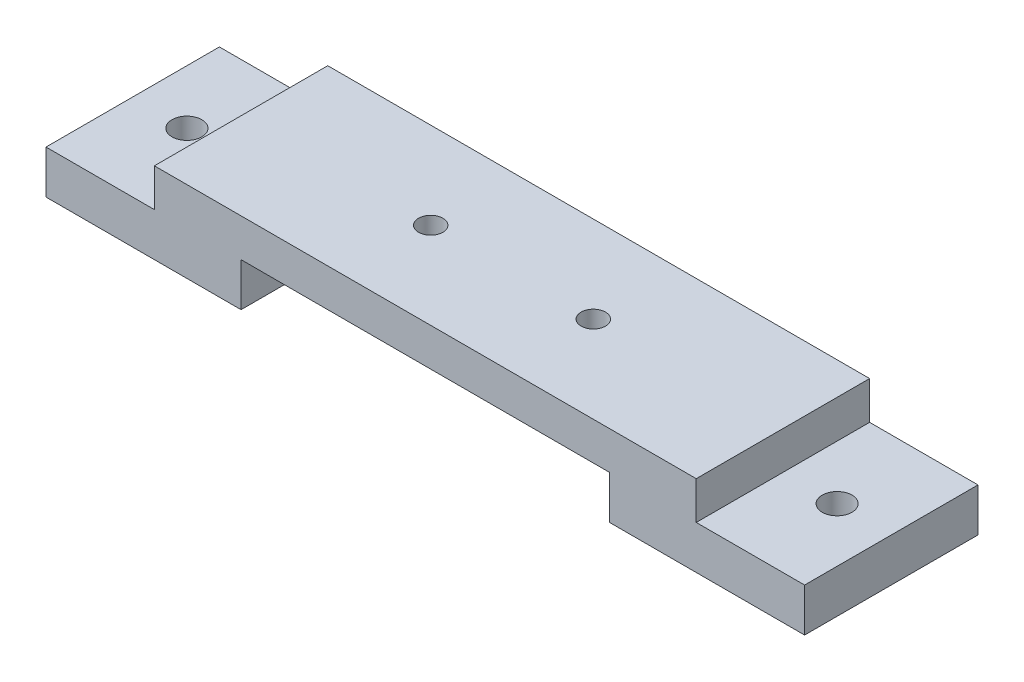
SolidWorks part; units mm, degrees
ref_plane "Ebene vorne" through (0, 0, 0) normal (0, 0, 1) x (1, 0, 0)
ref_plane "Ebene oben" through (0, 0, 0) normal (0, 1, 0) x (1, 0, 0)
ref_plane "Ebene rechts" through (0, 0, 0) normal (1, 0, 0) x (0, 0, -1)
sketch "Skizze1" plane through (0, 0, 0) normal (0, 0, 1) x (1, 0, 0)
  line L0 (-70, 20) -> (-34, 20)
  line L1 (-34, 20) -> (-34, 28)
  line L2 (-34, 28) -> (34, 28)
  line L3 (34, 28) -> (34, 20)
  line L4 (34, 20) -> (70, 20)
  line L5 (70, 20) -> (70, 28)
  line L6 (70, 28) -> (50, 28)
  line L7 (50, 28) -> (50, 35)
  line L8 (50, 35) -> (-50, 35)
  line L9 (-50, 35) -> (-50, 28)
  line L10 (-50, 28) -> (-70, 28)
  line L11 (-70, 28) -> (-70, 20)
  line L12 (34, 20) -> (34, 10) construction
  line L13 (50, 10) -> (70, 10) construction
  line L14 (34, 10) -> (-34, 10) construction
  line L15 (-50, 0) -> (50, 0) construction
  dimension "D2" = 8
  dimension "D3" = 8
  dimension "D4" = 7
extrude "Aufsatz-Linear austragen1" add sketch "Skizze1" against normal blind 32
hole_wizard "Ø4.5 (4.5) Durchmesser Bohrung1" positions "3D-Skizze1" profile "Skizze2" hole size "Ø4.5" standard "ANSI Metrisch" end condition through all
sketch3d "3D-Skizze1"
  line L0 (-34, 28, -16) -> (34, 28, -16) construction
  line L1 (-34, 28, -32) -> (-34, 28, 0) construction
  line L2 (34, 28, -32) -> (34, 28, 0) construction
  point P0 (-15, 28, -16)
  point P2 (15, 28, -16)
  dimension "D1" = 30
  dimension "D2" = 19
sketch "Skizze2" plane through (-15, 28, -16) normal (1, 0, 0) x (0, 0, -1)
  line L0 (0, 0) -> (0, 7)
  line L1 (0, 7) -> (2.25, 7)
  line L2 (2.25, 7) -> (2.25, 0)
  line L5 (2.25, 0) -> (0, 0)
  line L11 (0, -6.35) -> (0, 107.95) construction
  dimension "Bohrerdurchmesser" = 4.5
  dimension "Bohrungstiefe" = 7
hole_wizard "Ø5.5 (5.5) Durchmesser Bohrung1" positions "3D-Skizze2" profile "Skizze3" hole size "Ø5.5" standard "ANSI Metrisch" end condition through all
sketch3d "3D-Skizze2"
  line L0 (-50, 28, -32) -> (-70, 28, 0) construction
  line L2 (-70, 28, -32) -> (-50, 28, 0) construction
  line L4 (50, 28, -32) -> (70, 28, 0) construction
  line L6 (70, 28, -32) -> (50, 28, 0) construction
  point P0 (-60, 28, -16)
  point P2 (60, 28, -16)
  point P26 (0, 0, 0)
  point P27 (0, 0, 0)
sketch "Skizze3" plane through (-60, 28, -16) normal (1, 0, 0) x (0, 0, 1)
  line L0 (0, 0) -> (0, 8)
  line L1 (0, 8) -> (2.75, 8)
  line L2 (2.75, 8) -> (2.75, 0)
  line L5 (2.75, 0) -> (0, 0)
  line L11 (0, -6.35) -> (0, 107.95) construction
  dimension "Bohrerdurchmesser" = 5.5
  dimension "Bohrungstiefe" = 8
